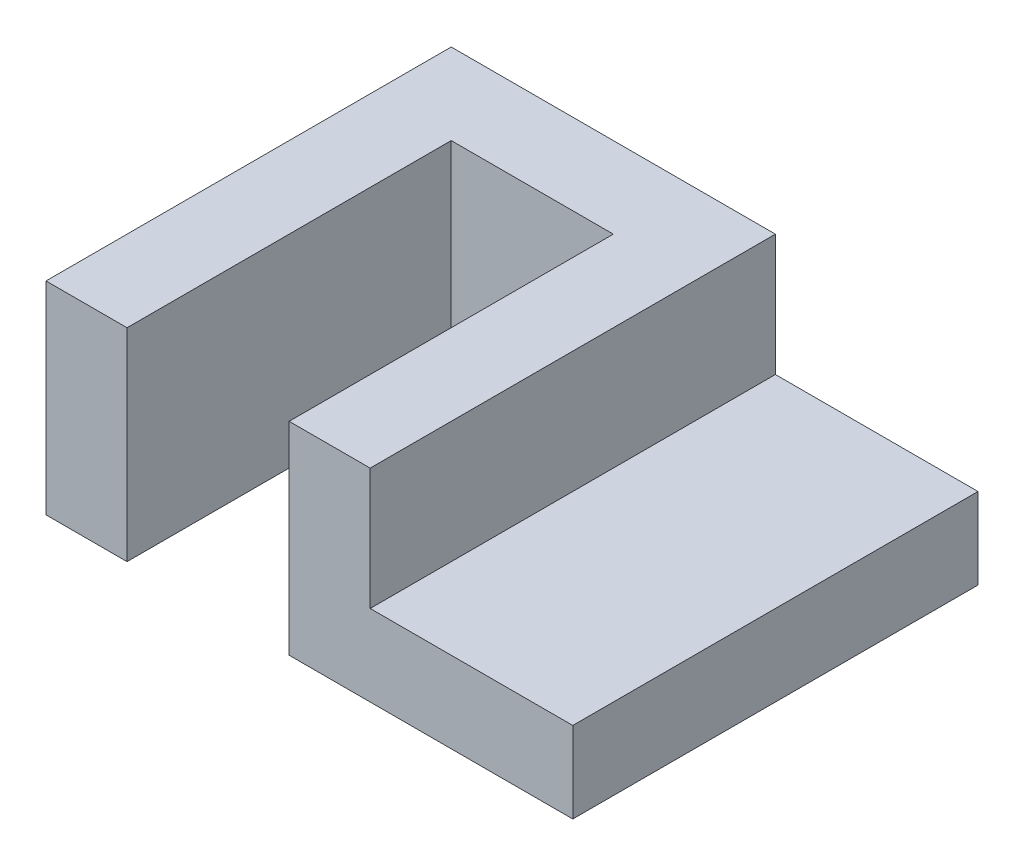
SolidWorks part; units mm, degrees
ref_plane "Front Plane" through (0, 0, 0) normal (0, 0, 1) x (1, 0, 0)
ref_plane "Top Plane" through (0, 0, 0) normal (0, 1, 0) x (1, 0, 0)
ref_plane "Right Plane" through (0, 0, 0) normal (1, 0, 0) x (0, 0, -1)
sketch "Sketch2" plane through (0, 0, 0) normal (0, 1, 0) x (1, 0, 0)
  line L0 (0, 0) -> (0, 100)
  line L1 (0, 100) -> (80, 100)
  line L2 (80, 100) -> (80, 0)
  line L3 (80, 0) -> (60, 0)
  line L4 (60, 0) -> (60, 80)
  line L5 (60, 80) -> (20, 80)
  line L6 (20, 80) -> (20, 0)
  line L7 (20, 0) -> (0, 0)
extrude "Boss-Extrude1" add sketch "Sketch2" along normal blind 50
sketch "Sketch3" plane through (80, 0, 0) normal (1, 0, 0) x (0, 0, -1)
  line L0 (100, 50) -> (100, 0) construction
  line L1 (0, 0) -> (100, 0)
  line L2 (0, 0) -> (0, 20)
  line L3 (0, 20) -> (100, 20)
  line L4 (100, 0) -> (100, 20)
extrude "Boss-Extrude2" add sketch "Sketch3" along normal blind 50
